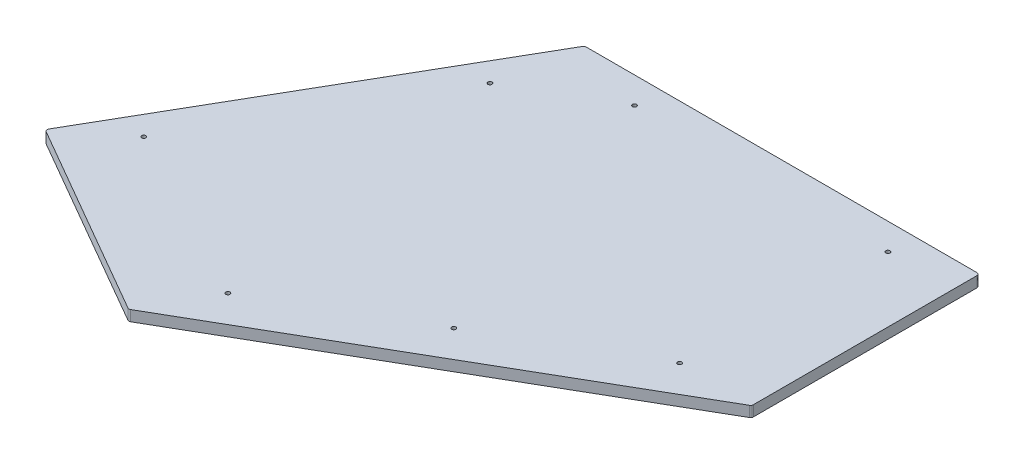
SolidWorks part; units mm, degrees
material "PE High Density"
ref_plane "Front Plane" through (0, 0, 0) normal (0, 0, 1) x (1, 0, 0)
ref_plane "Top Plane" through (0, 0, 0) normal (0, 1, 0) x (1, 0, 0)
ref_plane "Right Plane" through (0, 0, 0) normal (1, 0, 0) x (0, 0, -1)
sketch "Sketch1" plane through (0, 0, 0) normal (0, 1, 0) x (1, 0, 0)
  line L0 (42.5495, -468.9818) -> (384.8769, -271.3376) construction
  line L1 (-0.1992, -544.9894) -> (472.0751, -272.3199)
  line L2 (472.0751, -272.3199) -> (472.0751, -189.7062)
  line L3 (472.0751, 0) -> (0, 0)
  line L4 (0, 0) -> (-236.0363, -408.8297)
  line L5 (-236.0363, -408.8297) -> (-159.0465, -453.2795)
  line L6 (-169.6464, -357.3386) -> (-18.1641, -94.9618) construction
  line L7 (-18.1641, -94.9618) -> (91.3215, -31.7496) construction
  line L8 (91.3215, -31.7496) -> (394.2876, -31.7496) construction
  line L9 (394.2876, -31.7496) -> (384.8769, -271.3376) construction
  line L10 (-169.6464, -357.3386) -> (42.5495, -468.9818) construction
  line L11 (0, 0) -> (213.7132, -370.1597) construction
  line L12 (472.0751, -89.6938) -> (472.0751, 0)
  line L13 (472.0751, -89.6938) -> (508.5876, -89.6938) construction
  line L15 (472.0751, -189.7062) -> (508.5876, -189.7062) construction
  line L16 (508.5876, -89.6938) -> (508.5876, -189.7062) construction
  line L17 (-159.0465, -453.2795) -> (-139.9966, -420.2839) construction
  line L18 (-139.9966, -420.2839) -> (-52.0083, -471.0836) construction
  line L19 (-52.0083, -471.0836) -> (-71.0582, -504.0792) construction
  line L20 (-71.0582, -504.0792) -> (-0.1992, -544.9894)
  line L21 (-159.0465, -453.2795) -> (-71.0582, -504.0792)
  line L22 (472.0751, -89.6938) -> (472.0751, -189.7062)
  circle A0 centre (-169.6464, -357.3386) radius 2.4574
  circle A1 centre (-18.1641, -94.9618) radius 2.4574
  circle A2 centre (91.3215, -31.7496) radius 2.4574
  circle A3 centre (394.2876, -31.7496) radius 2.4574
  circle A4 centre (384.8769, -271.3376) radius 2.4575
  circle A5 centre (213.7132, -370.1597) radius 2.4575
  circle A6 centre (42.5495, -468.9818) radius 2.4575
  point P19 (36.5787, -63.3557)
  dimension "D12" = 4.9149
  dimension "D1" = 302.9661
  dimension "D2" = 302.9661
  dimension "D3" = 126.4234
  dimension "D4" = 77.7875
  dimension "D5" = 9.4107
  dimension "D6" = 239.588
  dimension "D7" = 239.7735
  dimension "D8" = 111.6432
  dimension "D9" = 100.0125
  dimension "D10" = 77.7875
  dimension "D11" = 44.45
  dimension "D13" = 89.6938
  dimension "D14" = 31.75
  dimension "D15" = 36.5125
  dimension "D16" = 38.1
  dimension "D17" = 101.6
  dimension "D18" = 88.9
extrude "Boss-Extrude1" add sketch "Sketch1" along normal blind 12.7
fillet "Fillet1" radius 3.175 5 edges at (472.0751, 6.35, 272.3199) (-0.1992, 6.35, 544.9894) (-236.0363, 6.35, 408.8297) (0, 6.35, 0) (472.0751, 6.35, 0)
